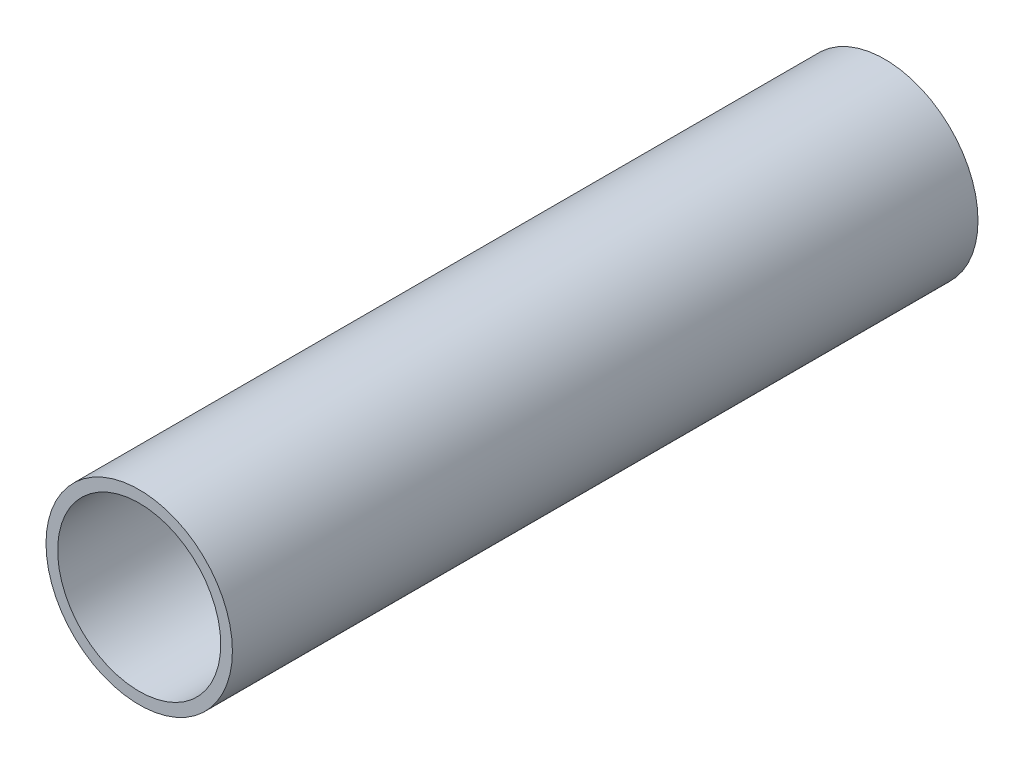
SolidWorks part; units mm, degrees
material "PVC Rigid"
ref_plane "Front Plane" through (0, 0, 0) normal (0, 0, 1) x (1, 0, 0)
ref_plane "Top Plane" through (0, 0, 0) normal (0, 1, 0) x (1, 0, 0)
ref_plane "Right Plane" through (0, 0, 0) normal (1, 0, 0) x (0, 0, -1)
sketch "Sketch1" plane through (0, 0, 0) normal (0, 0, 1) x (1, 0, 0)
  circle A0 centre (0, 0) radius 12.7
  circle A1 centre (0, 0) radius 11.1125
  dimension "D1" = 25.4
  dimension "D2" = 22.225
extrude "Boss-Extrude1" add sketch "Sketch1" along normal blind 101.6
